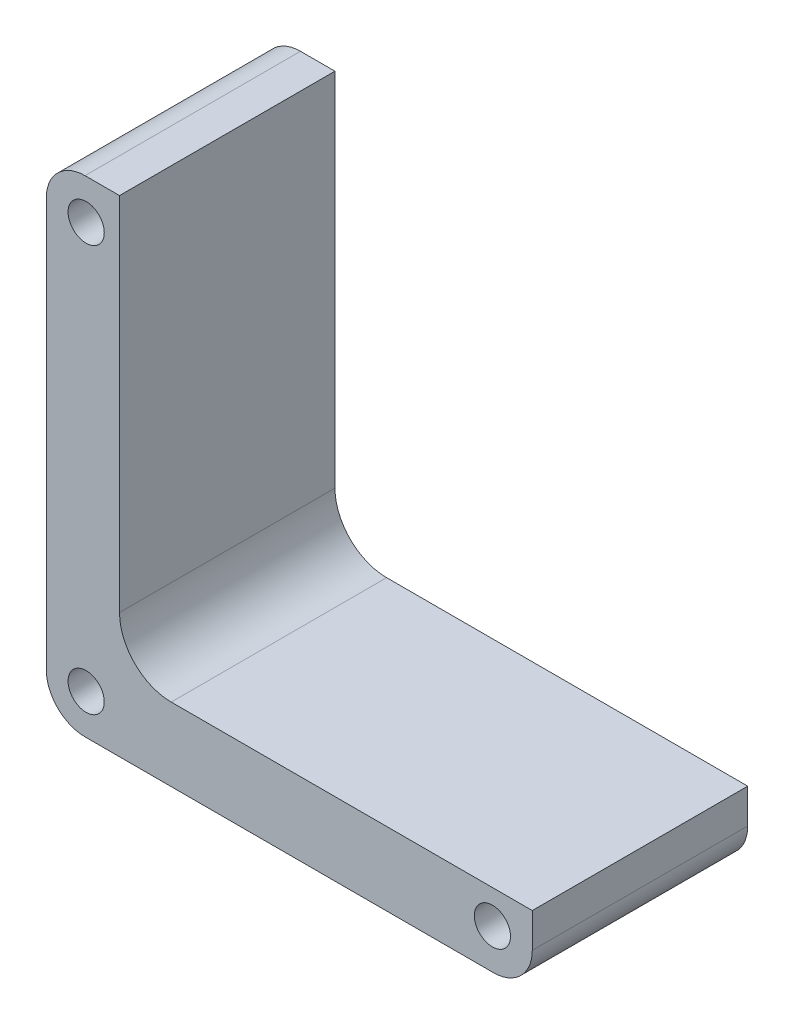
SolidWorks part; units mm, degrees
material "Alumine"
ref_plane "Plan de face" through (0, 0, 0) normal (0, 0, 1) x (1, 0, 0)
ref_plane "Plan de dessus" through (0, 0, 0) normal (0, 1, 0) x (1, 0, 0)
ref_plane "Plan de droite" through (0, 0, 0) normal (1, 0, 0) x (0, 0, -1)
sketch "Esquisse1" plane through (0, 0, 0) normal (0, 0, 1) x (1, 0, 0)
  line L1 (-28.2, -28.2) -> (28.2, -28.2)
  line L2 (-28.2, -28.2) -> (-28.2, 28.2)
  line L3 (-28.2, 28.2) -> (28.2, 28.2)
  line L4 (28.2, -28.2) -> (28.2, 28.2)
  line L5 (0, 28.2) -> (0, -28.2) construction
  line L6 (-28.2, 0) -> (28.2, 0) construction
  point P0 (0, 0)
  dimension "D1" = 56.4
  dimension "D2" = 56.4
extrude "Boss.-Extru.1" add sketch "Esquisse1" along normal blind 25
sketch "Esquisse2" plane through (0, 0, 25) normal (0, 0, 1) x (1, 0, 0)
  line L0 (0, 0) -> (46.3367, 45.5841) construction
  line L1 (-7.3383, 4.2895) -> (24.3219, 58.4525) construction
  line L2 (4.1687, -7.4075) -> (58.8429, 23.3615) construction
  line L3 (-28.2, 28.2) -> (-28.2, -28.2) construction
  line L4 (-19.7, -19.7) -> (56.1735, -19.7)
  line L5 (-19.7, -19.7) -> (-19.7, 51.2516)
  line L6 (-19.7, 51.2516) -> (56.1735, 51.2516)
  line L7 (56.1735, -19.7) -> (56.1735, 51.2516)
  line L8 (-28.2, -28.2) -> (28.2, -28.2) construction
  circle A0 centre (0, 0) radius 8.5 construction
  circle A1 centre (46.3367, 45.5841) radius 25.5 construction
  dimension "D1" = 17
  dimension "D3" = 51
  dimension "D2" = 65
  dimension "D4" = 8.5
  dimension "D5" = 8.5
extrude "Enlèv. mat.-Extru.1" cut sketch "Esquisse2" against normal through all
hole_wizard "Trou pour taraudage pour trou taraudé M51" positions "Esquisse3" profile "Esquisse4" hole size "M5" standard "ISO" end condition through all
sketch "Esquisse3" plane through (0, 0, 25) normal (0, 0, 1) x (1, 0, 0)
  line L1 (-23.57, -23.57) -> (23.57, -23.57)
  line L2 (-23.57, -23.57) -> (-23.57, 23.57)
  line L3 (-23.57, 23.57) -> (23.57, 23.57)
  line L4 (23.57, -23.57) -> (23.57, 23.57)
  line L5 (0, 23.57) -> (0, -23.57) construction
  line L6 (-23.57, 0) -> (23.57, 0) construction
  line L7 (-28.2, 28.2) -> (-28.2, -28.2) construction
  line L8 (-28.2, -28.2) -> (28.2, -28.2) construction
  line L11 (28.2, -28.2) -> (28.2, -19.7) construction
  point P1 (23.57, 23.57)
  point P8 (-23.57, -23.57)
  point P9 (-23.57, 23.57)
  point P10 (23.57, -23.57)
  dimension "D1" = 4.63
  dimension "D2" = 4.63
  dimension "D3" = 4.63
sketch "Esquisse4" plane through (23.57, 23.57, 25) normal (1, 0, 0) x (0, -1, 0)
  line L0 (0, 0) -> (0, 25)
  line L1 (0, 25) -> (2.1, 25)
  line L2 (2.1, 25) -> (2.1, 0)
  line L5 (2.1, 0) -> (0, 0)
  line L11 (0, -6.35) -> (0, 107.95) construction
  dimension "Diamètre du perçage jusqu'au prochain" = 4.2
  dimension "Profondeur du perçage jusqu'au prochain" = 25
fillet "Congé1" radius 6 1 edges at (-19.7, -19.7, 12.5)
fillet "Congé2" radius 4.5 3 edges at (-28.2, 28.2, 12.5) (28.2, -28.2, 12.5) (-28.2, -28.2, 12.5)
